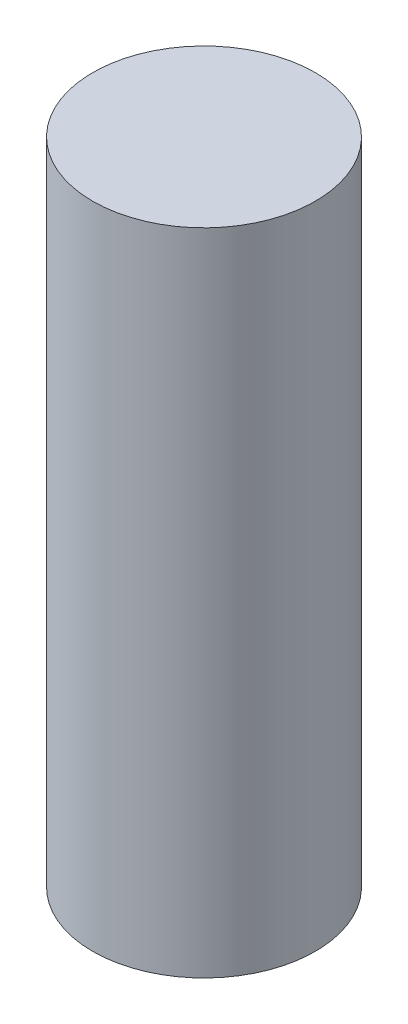
SolidWorks part; units mm, degrees
ref_plane "Front" through (0, 0, 0) normal (0, 0, 1) x (1, 0, 0)
ref_plane "Top" through (0, 0, 0) normal (0, 1, 0) x (1, 0, 0)
ref_plane "Right" through (0, 0, 0) normal (1, 0, 0) x (0, 0, -1)
sketch "Sketch1" plane through (0, 0, 0) normal (0, 1, 0) x (1, 0, 0)
  circle A0 centre (-15.7661, 9.8538) radius 6
extrude "Boss-Extrude1" add sketch "Sketch1" along normal blind 35
